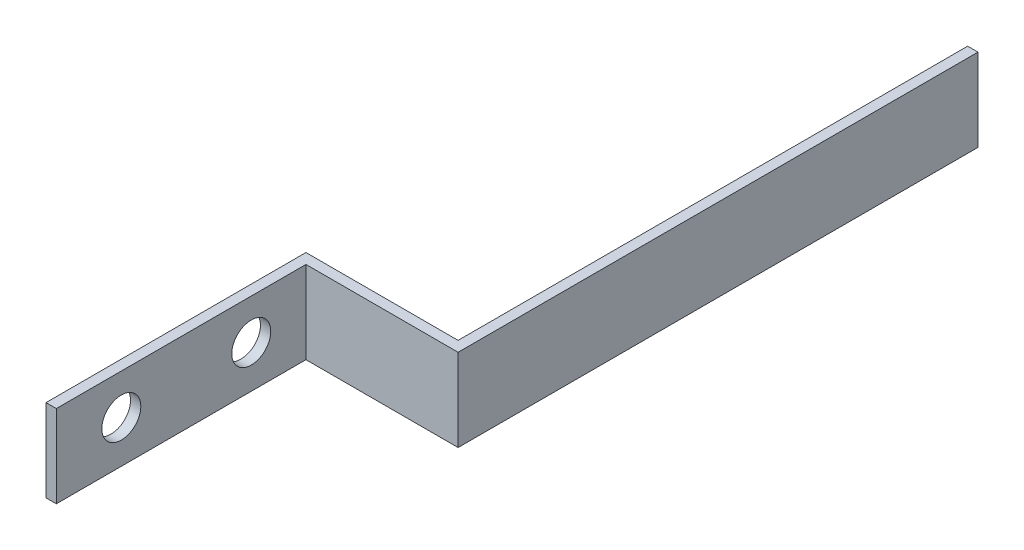
SolidWorks part; units mm, degrees
ref_plane "Front Plane" through (0, 0, 0) normal (0, 0, 1) x (1, 0, 0)
ref_plane "Top Plane" through (0, 0, 0) normal (0, 1, 0) x (1, 0, 0)
ref_plane "Right Plane" through (0, 0, 0) normal (1, 0, 0) x (0, 0, -1)
sketch "Sketch1" plane through (0, 0, 0) normal (0, 1, 0) x (1, 0, 0)
  line L0 (0, 0) -> (0, 80)
  line L1 (0, 80) -> (46.825, 80)
  line L2 (46.825, 80) -> (46.825, 236.825)
  line L3 (46.825, 236.825) -> (50, 236.825)
  line L4 (50, 236.825) -> (50, 76.825)
  line L5 (50, 76.825) -> (3.175, 76.825)
  line L6 (3.175, 76.825) -> (3.175, 0)
  line L7 (3.175, 0) -> (0, 0)
  dimension "D1" = 80
  dimension "D2" = 76.825
  dimension "D3" = 3.175
  dimension "D4" = 3.175
  dimension "D5" = 46.825
  dimension "D6" = 160
extrude "Boss-Extrude1" add sketch "Sketch1" along normal blind 25.4
sketch "Sketch2" plane through (3.175, 0, 0) normal (1, 0, 0) x (0, 0, -1)
  line L0 (20, 13) -> (60, 13)
  line L1 (0, 0) -> (20, 0)
  line L2 (0, 0) -> (0, 13)
  line L3 (0, 13) -> (20, 13)
  line L4 (20, 0) -> (20, 13)
  circle A0 centre (60, 13) radius 6
  circle A1 centre (20, 13) radius 6
  dimension "D1" = 13
  dimension "D2" = 20
  dimension "D3" = 40
extrude "Cut-Extrude1" cut sketch "Sketch2" against normal blind 25.4 contours A0 | A1
